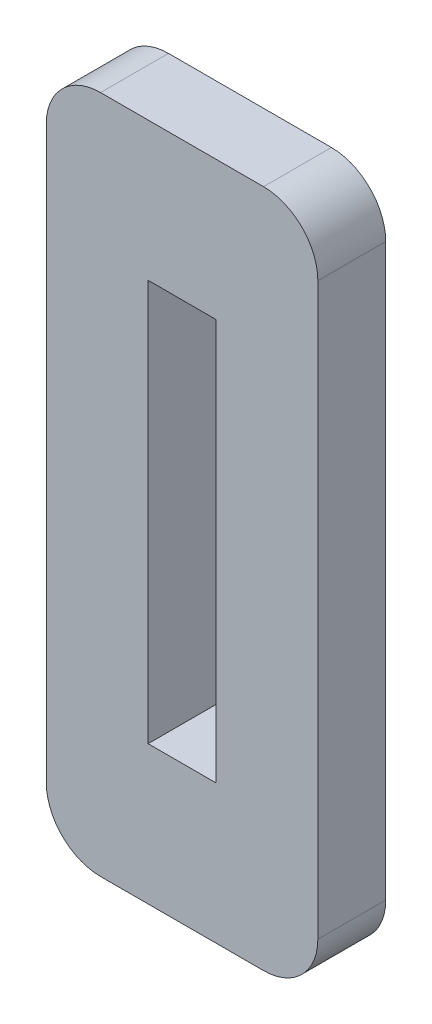
SolidWorks part; units mm, degrees
ref_plane "Alzado" through (0, 0, 0) normal (0, 0, 1) x (1, 0, 0)
ref_plane "Planta" through (0, 0, 0) normal (0, 1, 0) x (1, 0, 0)
ref_plane "Vista lateral" through (0, 0, 0) normal (1, 0, 0) x (0, 0, -1)
sketch "Croquis1" plane through (0, 0, 0) normal (0, 0, 1) x (1, 0, 0)
  line L1 (-1.25, 7.3886) -> (1.25, 7.3886)
  line L2 (-1.25, 7.3886) -> (-1.25, -7.3886)
  line L3 (-1.25, -7.3886) -> (1.25, -7.3886)
  line L4 (1.25, 7.3886) -> (1.25, -7.3886)
  line L5 (-1.25, 7.3886) -> (1.25, -7.3886) construction
  line L6 (-1.25, -7.3886) -> (1.25, 7.3886) construction
  line L7 (-5, 12.5) -> (5, 12.5)
  line L8 (-5, 12.5) -> (-5, -12.5)
  line L9 (-5, -12.5) -> (5, -12.5)
  line L10 (5, 12.5) -> (5, -12.5)
  line L11 (-5, 12.5) -> (5, -12.5) construction
  line L12 (-5, -12.5) -> (5, 12.5) construction
  point P0 (0, 0)
  point P6 (0, 0)
  dimension "D1" = 14.7772
  dimension "D2" = 2.5
  dimension "D3" = 10
  dimension "D4" = 25
extrude "Saliente-Extruir1" add sketch "Croquis1" along normal blind 2.5
fillet "Redondeo1" radius 2 4 edges at (5, -12.5, 1.25) (-5, -12.5, 1.25) (-5, 12.5, 1.25) (5, 12.5, 1.25)
